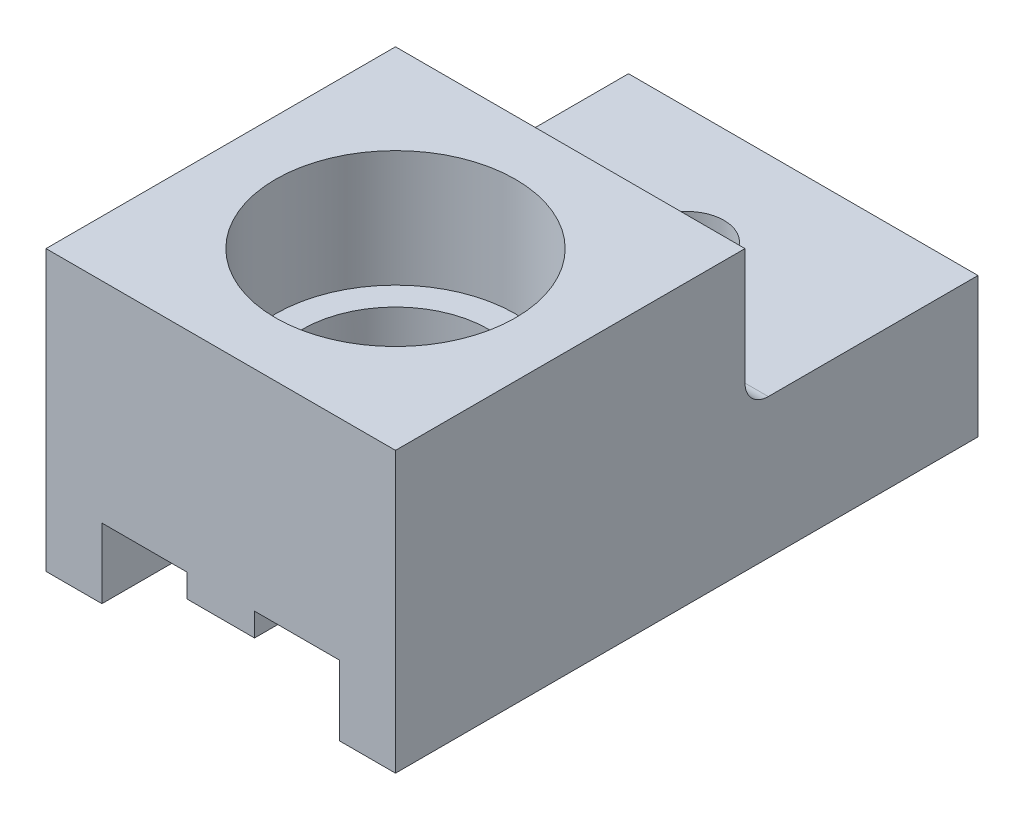
SolidWorks part; units mm, degrees
ref_plane "Front Plane" through (0, 0, 0) normal (0, 0, 1) x (1, 0, 0)
ref_plane "Top Plane" through (0, 0, 0) normal (0, 1, 0) x (1, 0, 0)
ref_plane "Right Plane" through (0, 0, 0) normal (1, 0, 0) x (0, 0, -1)
sketch "Sketch1" plane through (0, 0, 0) normal (0, 0, 1) x (1, 0, 0)
  line L0 (-5.1, 0) -> (-5.1, -3)
  line L1 (-5.1, 0) -> (-1.45, 0)
  line L2 (-1.45, 0) -> (-1.45, -1)
  line L3 (-1.45, -1) -> (1.45, -1)
  line L4 (1.45, -1) -> (1.45, 0)
  line L5 (1.45, 0) -> (5.1, 0)
  line L6 (5.1, 0) -> (5.1, -3)
  line L7 (7.5, 9) -> (-7.5, 9)
  line L8 (-5.1, -3) -> (-7.5, -3)
  line L9 (-7.5, -3) -> (-7.5, 9)
  line L10 (5.1, -3) -> (7.5, -3)
  line L11 (7.5, -3) -> (7.5, 9)
  point P0 (0, -1)
  dimension "D1" = 2.9
  dimension "D2" = 10.2
  dimension "D3" = 1
  dimension "D4" = 3
  dimension "D5" = 12
  dimension "D6" = 15
extrude "Main" add sketch "Sketch1" along normal blind 25
sketch "Sketch2" plane through (0, 9, 0) normal (0, 1, 0) x (1, 0, 0)
  line L0 (7.5, -25) -> (-7.5, -25) construction
  circle A0 centre (0, -17.5) radius 5.15
  dimension "D1" = 10.3
  dimension "D2" = 7.5
extrude "RollingHole" cut sketch "Sketch2" against normal blind 5
sketch "Sketch3" plane through (0, 4, 0) normal (0, 1, 0) x (1, 0, 0)
  circle A0 centre (0, -17.5) radius 4
  circle A2 centre (0, -17.5) radius 5.15 construction
  dimension "D1" = 8
extrude "Cut-Extrude2" cut sketch "Sketch3" against normal through all
sketch "Sketch4" plane through (0, 9, 0) normal (0, 1, 0) x (1, 0, 0)
  circle A0 centre (0, -5) radius 1.6
  dimension "D1" = 3.2
  dimension "D2" = 5
extrude "FixHole" cut sketch "Sketch4" against normal through all
sketch "Sketch5" plane through (-7.5, 0, 0) normal (-1, 0, 0) x (0, 0, 1)
  line L1 (0, 9) -> (10, 9)
  line L2 (0, 9) -> (0, 3)
  line L3 (0, 3) -> (10, 3)
  line L4 (10, 9) -> (10, 3)
  dimension "D1" = 3
  dimension "D2" = 10
extrude "Cut-Extrude4" cut sketch "Sketch5" against normal through all
fillet "Fillet1" radius 1 1 edges at (0, 3, 10)
